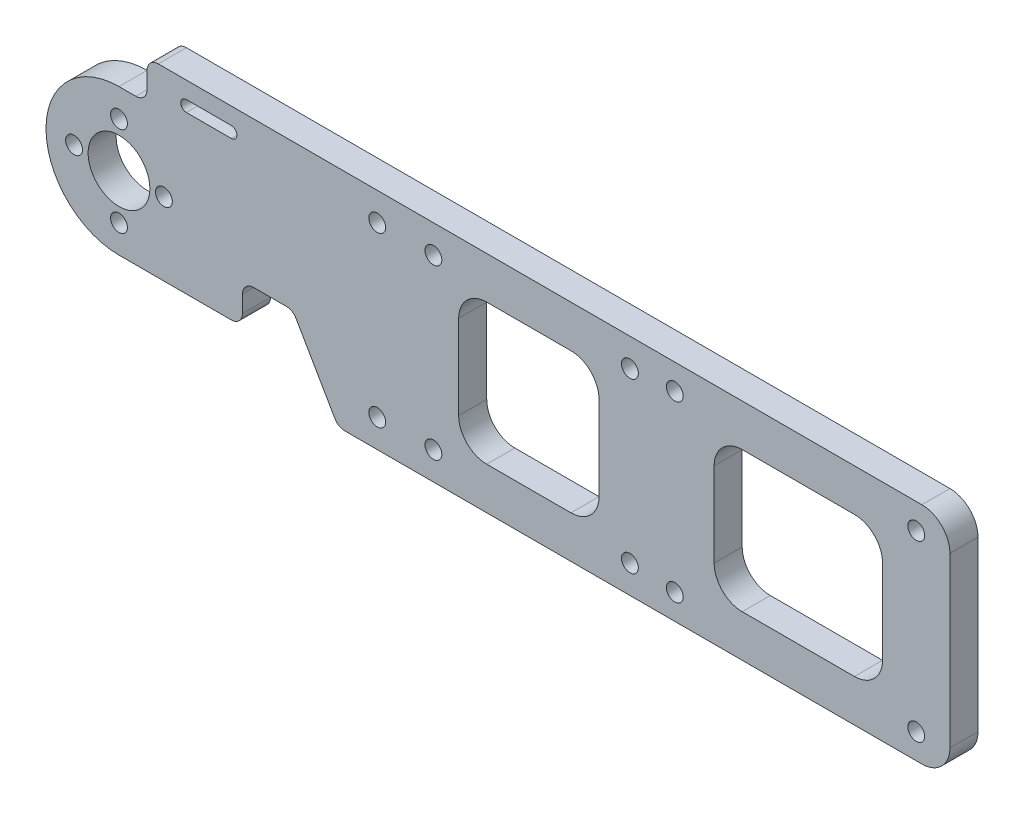
SolidWorks part; units mm, degrees
material "Acrylic (Medium-high impact)"
ref_plane "Front Plane" through (0, 0, 0) normal (0, 0, 1) x (1, 0, 0)
ref_plane "Top Plane" through (0, 0, 0) normal (0, 1, 0) x (1, 0, 0)
ref_plane "Right Plane" through (0, 0, 0) normal (1, 0, 0) x (0, 0, -1)
sketch "Sketch2" plane through (0, 0, 0) normal (0, 0, 1) x (1, 0, 0)
  line L0 (0, 20) -> (0, -20)
  line L1 (0, 20) -> (148, 20)
  line L2 (0, -20) -> (148, -20)
  line L3 (148, 20) -> (148, -20)
  line L4 (0, 0) -> (-17, 0)
  line L5 (0, -13) -> (35, -13)
  line L6 (35, -13) -> (35, -20)
  line L7 (5, 13) -> (22, -6)
  line L8 (0, 13) -> (5, 13)
  line L9 (0, 13) -> (0, 20)
  line L10 (0, 20) -> (5, 20)
  line L11 (5, 13) -> (5, 20)
  line L12 (35, -13) -> (39.0415, -20)
  line L13 (22, -13) -> (35, -13)
  line L14 (22, -13) -> (22, -6)
  line L15 (22, -6) -> (35, -6)
  line L16 (35, -13) -> (35, -6)
  line L17 (35, -13) -> (30.9585, -6)
  circle A1 centre (0, 0) radius 5.5
  circle A2 centre (0, 0) radius 13
  dimension "D1" = 148
  dimension "D3" = 11
  dimension "D6" = 26
  dimension "D2" = 165
  dimension "D4" = 40
  dimension "D5" = 20
  dimension "D7" = 35
  dimension "D8" = 22
  dimension "D9" = 7
  dimension "D10" = 5
  dimension "D11" = 60
  dimension "D12" = 60
extrude "Boss-Extrude1" add sketch "Sketch2" along normal mid plane 5
fillet "Fillet1" radius 5 2 edges at (148, -20, 0) (148, 20, 0)
sketch "Sketch3" plane through (0, 0, -2.5) normal (0, 0, -1) x (-1, 0, 0)
  line L0 (-83, 0) -> (-119.5, 0)
  line L1 (-142, 0) -> (-99, 0)
  line L2 (-91, 15) -> (-91, 0)
  line L3 (-119.5, 0) -> (-148, 0)
  line L4 (-142, 0) -> (-142, 15.5)
  line L5 (-99, 0) -> (-99, 15.5)
  line L12 (0, 0) -> (0, 15.666)
  line L13 (0, 0) -> (-83, 0)
  line L14 (-20, 16) -> (-12, 16) construction
  line L17 (-20, 17) -> (-12, 17)
  line L18 (-20, 15) -> (-12, 15)
  line L19 (0, 0) -> (18.4819, 0)
  line L24 (-22, -6) -> (-22, -13)
  line L25 (-148, 15) -> (-148, -15)
  line L27 (-148, 15) -> (-148, -15)
  line L29 (-143, -20) -> (-39.0415, -20)
  line L31 (-143, -20) -> (-39.0415, -20)
  line L33 (-5, 20) -> (-143, 20)
  line L35 (-5, 20) -> (-143, 20)
  line L36 (-39.0415, -20) -> (-30.9585, -6)
  line L38 (-22, -13) -> (0, -13)
  line L39 (-22, -13) -> (0, -13)
  line L40 (0, 13) -> (-5, 13)
  line L41 (0, 13) -> (-5, 13)
  line L42 (-5, 13) -> (-5, 20)
  line L43 (-5, 13) -> (-5, 20)
  line L44 (-30.9585, -6) -> (-22, -6)
  line L45 (-30.9585, -6) -> (-22, -6)
  line L46 (-22, -6) -> (-22, -13)
  line L49 (-39.0415, -20) -> (-30.9585, -6)
  circle A3 centre (-56, -15) radius 1.5
  arc A4 (0, -13) -> (0, 13) centre (0, 0) ccw
  circle A12 centre (-91, -15) radius 1.5
  circle A13 centre (-46, -15) radius 1.5
  arc A21 (-20, 17) -> (-20, 15) centre (-20, 16) ccw
  arc A22 (-12, 15) -> (-12, 17) centre (-12, 16) ccw
  circle A24 centre (-91, 15) radius 1.5
  circle A26 centre (-46, 15) radius 1.5
  circle A27 centre (0, 0) radius 8
  circle A28 centre (0, -8) radius 1.5
  circle A29 centre (-8, 0) radius 1.5
  circle A30 centre (0, 8) radius 1.5
  circle A31 centre (8, 0) radius 1.5
  circle A32 centre (-56, 15) radius 1.5
  arc A33 (-148, -15) -> (-143, -20) centre (-143, -15) ccw
  arc A34 (-148, -15) -> (-143, -20) centre (-143, -15) ccw
  arc A35 (-143, 20) -> (-148, 15) centre (-143, 15) ccw
  arc A36 (-143, 20) -> (-148, 15) centre (-143, 15) ccw
  circle A37 centre (-142, 15.5) radius 1.5
  circle A38 centre (-99, 15.5) radius 1.5
  arc A42 (0, -13) -> (0, 13) centre (0, 0) ccw
  circle A43 centre (-142, -15.5) radius 1.5
  circle A44 centre (-99, -15.5) radius 1.5
  point P35 (-16, 16)
  point P48 (15.666, 0)
  point P53 (-12, 0)
  point P54 (-7.6279, -12)
  dimension "D6" = 51
  dimension "D10" = 15
  dimension "D11" = 16
  dimension "D13" = 45
  dimension "D17" = 3
  dimension "D18" = 4
  dimension "D12" = 3
  dimension "D19" = 16
  dimension "D21" = 3
  dimension "D22" = 3
  dimension "D5" = 3
  dimension "D24" = 3
  dimension "D3" = 43
  dimension "D4" = 15.5
  dimension "D7" = 15
  dimension "D8" = 30
  dimension "D9" = 16
  dimension "D14" = 8
  dimension "D15" = 2
  dimension "D16" = 16
  dimension "D20" = 35
  dimension "D23" = 15.5
  dimension "D1" = 0
extrude "Cut-Extrude1" cut sketch "Sketch3" against normal through all
fillet "Fillet2" radius 2 6 edges at (5, 20, 0) (5, 13, 0) (22, -13, 0) (22, -6, 0) (39.0415, -20, 0) (30.9585, -6, 0)
sketch "Sketch4" plane through (0, 0, 2.5) normal (0, 0, 1) x (1, 0, 0)
  line L1 (55, 0) -> (148, 0)
  line L2 (91, 15) -> (91, -15)
  line L4 (85.5, -12.5) -> (60.5, -12.5)
  line L9 (31.5359, -7) -> (38.4641, -19)
  line L10 (40.1962, -20) -> (143, -20)
  line L11 (148, -15) -> (148, 15)
  line L12 (143, 20) -> (7, 20)
  line L13 (5, 18) -> (5, 15)
  line L14 (3, 13) -> (0, 13)
  line L15 (0, -13) -> (20, -13)
  line L16 (22, -11) -> (22, -8)
  line L17 (24, -6) -> (29.8038, -6)
  line L18 (31.5359, -7) -> (38.4641, -19)
  line L19 (40.1962, -20) -> (143, -20)
  line L20 (148, -15) -> (148, 15)
  line L21 (143, 20) -> (7, 20)
  line L22 (5, 18) -> (5, 15)
  line L23 (3, 13) -> (0, 13)
  line L24 (0, -13) -> (20, -13)
  line L25 (22, -11) -> (22, -8)
  line L26 (24, -6) -> (29.8038, -6)
  line L27 (85.5, -12.5) -> (85.5, 12.5)
  line L28 (85.5, 12.5) -> (60.5, 12.5)
  line L33 (60.5, -12.5) -> (60.5, 12.5)
  line L34 (85.5, -12.5) -> (60.5, 12.5) construction
  line L35 (85.5, 12.5) -> (60.5, -12.5) construction
  line L36 (106, 12.5) -> (136, 12.5)
  line L37 (106, 12.5) -> (106, -12.5)
  line L38 (106, -12.5) -> (136, -12.5)
  line L39 (136, 12.5) -> (136, -12.5)
  line L40 (106, 12.5) -> (136, -12.5) construction
  line L41 (106, -12.5) -> (136, 12.5) construction
  arc A9 (38.4641, -19) -> (40.1962, -20) centre (40.1962, -18) ccw
  arc A10 (143, -20) -> (148, -15) centre (143, -15) ccw
  arc A11 (148, 15) -> (143, 20) centre (143, 15) ccw
  arc A12 (7, 20) -> (5, 18) centre (7, 18) ccw
  arc A13 (3, 13) -> (5, 15) centre (3, 15) ccw
  arc A14 (0, 13) -> (0, -13) centre (0, 0) ccw
  arc A15 (20, -13) -> (22, -11) centre (20, -11) ccw
  arc A16 (24, -6) -> (22, -8) centre (24, -8) ccw
  arc A17 (31.5359, -7) -> (29.8038, -6) centre (29.8038, -8) ccw
  arc A18 (38.4641, -19) -> (40.1962, -20) centre (40.1962, -18) ccw
  arc A19 (143, -20) -> (148, -15) centre (143, -15) ccw
  arc A20 (148, 15) -> (143, 20) centre (143, 15) ccw
  arc A21 (7, 20) -> (5, 18) centre (7, 18) ccw
  arc A22 (3, 13) -> (5, 15) centre (3, 15) ccw
  arc A23 (0, 13) -> (0, -13) centre (0, 0) ccw
  arc A24 (20, -13) -> (22, -11) centre (20, -11) ccw
  arc A25 (24, -6) -> (22, -8) centre (24, -8) ccw
  arc A26 (31.5359, -7) -> (29.8038, -6) centre (29.8038, -8) ccw
  point P27 (73, 0)
  point P35 (121, 0)
  dimension "D2" = 18
  dimension "D3" = 30
  dimension "D4" = 25
  dimension "D5" = 25
  dimension "D6" = 25
  dimension "D7" = 30
  dimension "D1" = 0
extrude "Cut-Extrude2" cut sketch "Sketch4" against normal blind 10 contours L33 L1 L27 L28 | L33 L4 L27 L1 | L39 L36 L37 L1 | L39 L1 L37 L38
fillet "Fillet3" radius 5 8 edges at (136, 12.5, 0) (106, 12.5, 0) (136, -12.5, 0) (106, -12.5, 0) (85.5, -12.5, 0) (85.5, 12.5, 0) (60.5, -12.5, 0) (60.5, 12.5, 0)
sketch "Sketch5" plane through (0, 0, -2.5) normal (0, 0, -1) x (-1, 0, 0)
  line L9 (-143, -20) -> (-40.1962, -20)
  line L10 (-38.4641, -19) -> (-31.5359, -7)
  line L11 (-29.8038, -6) -> (-24, -6)
  line L12 (-22, -8) -> (-22, -11)
  line L13 (-20, -13) -> (0, -13)
  line L14 (0, 13) -> (-3, 13)
  line L15 (-5, 15) -> (-5, 18)
  line L16 (-7, 20) -> (-143, 20)
  line L17 (-148, 15) -> (-148, -15)
  line L18 (-143, -20) -> (-40.1962, -20)
  line L19 (-38.4641, -19) -> (-31.5359, -7)
  line L20 (-29.8038, -6) -> (-24, -6)
  line L21 (-22, -8) -> (-22, -11)
  line L22 (-20, -13) -> (0, -13)
  line L23 (0, 13) -> (-3, 13)
  line L24 (-5, 15) -> (-5, 18)
  line L25 (-7, 20) -> (-143, 20)
  line L26 (-148, 15) -> (-148, -15)
  circle A0 centre (-99, -15.5) radius 2.5
  circle A1 centre (-99, 15.5) radius 2.5
  arc A9 (-40.1962, -20) -> (-38.4641, -19) centre (-40.1962, -18) ccw
  arc A10 (-29.8038, -6) -> (-31.5359, -7) centre (-29.8038, -8) ccw
  arc A11 (-22, -8) -> (-24, -6) centre (-24, -8) ccw
  arc A12 (-22, -11) -> (-20, -13) centre (-20, -11) ccw
  arc A13 (0, -13) -> (0, 13) centre (0, 0) ccw
  arc A14 (-5, 15) -> (-3, 13) centre (-3, 15) ccw
  arc A15 (-5, 18) -> (-7, 20) centre (-7, 18) ccw
  arc A16 (-143, 20) -> (-148, 15) centre (-143, 15) ccw
  arc A17 (-148, -15) -> (-143, -20) centre (-143, -15) ccw
  arc A18 (-40.1962, -20) -> (-38.4641, -19) centre (-40.1962, -18) ccw
  arc A19 (-29.8038, -6) -> (-31.5359, -7) centre (-29.8038, -8) ccw
  arc A20 (-22, -8) -> (-24, -6) centre (-24, -8) ccw
  arc A21 (-22, -11) -> (-20, -13) centre (-20, -11) ccw
  arc A22 (0, -13) -> (0, 13) centre (0, 0) ccw
  arc A23 (-5, 15) -> (-3, 13) centre (-3, 15) ccw
  arc A24 (-5, 18) -> (-7, 20) centre (-7, 18) ccw
  arc A25 (-143, 20) -> (-148, 15) centre (-143, 15) ccw
  arc A26 (-148, -15) -> (-143, -20) centre (-143, -15) ccw
  dimension "D2" = 5
  dimension "D3" = 5
  dimension "D1" = 0
extrude "Cut-Extrude3" cut sketch "Sketch5" against normal blind 2 contours A1 | A0
